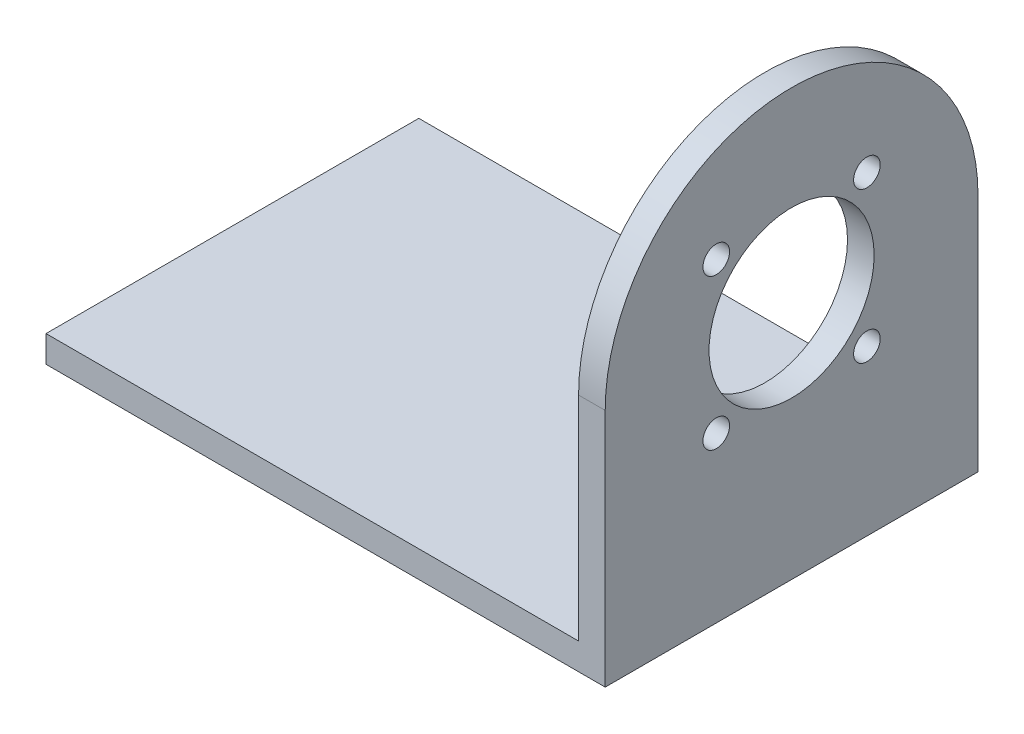
SolidWorks part; units mm, degrees
material "Alloy Steel"
ref_plane "Front Plane" through (0, 0, 0) normal (0, 0, 1) x (1, 0, 0)
ref_plane "Top Plane" through (0, 0, 0) normal (0, 1, 0) x (1, 0, 0)
ref_plane "Right Plane" through (0, 0, 0) normal (1, 0, 0) x (0, 0, -1)
sketch "Sketch1" plane through (0, 0, 0) normal (0, 1, 0) x (1, 0, 0)
  line L1 (-52.5, -35) -> (52.5, -35)
  line L2 (-52.5, -35) -> (-52.5, 35)
  line L3 (-52.5, 35) -> (52.5, 35)
  line L4 (52.5, -35) -> (52.5, 35)
  line L5 (-52.5, -35) -> (52.5, 35) construction
  line L6 (-52.5, 35) -> (52.5, -35) construction
  point P0 (0, 0)
  dimension "D1" = 70
  dimension "D2" = 105
extrude "Boss-Extrude1" add sketch "Sketch1" along normal blind 5
sketch "Sketch2" plane through (0, 5, 0) normal (0, 1, 0) x (1, 0, 0)
  line L0 (-52.5, -35) -> (52.5, -35) construction
  line L1 (52.5, 35) -> (47.5, 35)
  line L2 (52.5, 35) -> (52.5, -35)
  line L3 (52.5, -35) -> (47.5, -35)
  line L4 (47.5, 35) -> (47.5, -35)
  dimension "D1" = 5
extrude "Boss-Extrude2" add sketch "Sketch2" along normal blind 70
sketch "Sketch3" plane through (47.5, 0, 0) normal (-1, 0, 0) x (0, 0, 1)
  line L0 (-35, 75) -> (-35, 5) construction
  line L1 (-35, 75) -> (-35, 45)
  line L2 (35, 75) -> (35, 5) construction
  line L3 (35, 75) -> (35, 45)
  line L4 (0, 29.9331) -> (0, 64.3237) construction
  line L5 (-25.6841, 45) -> (12.1891, 45) construction
  line L6 (-35, 75) -> (35, 75) construction
  line L7 (-35, 75) -> (35, 75)
  arc A0 (35, 45) -> (-35, 45) centre (0, 45) ccw
  line M6 (35, 5) -> (35, 75)
  line M7 (35, 75) -> (-35, 75)
  line M8 (-35, 75) -> (-35, 5)
  dimension "D1" = 70
extrude "Cut-Extrude1" cut sketch "Sketch3" against normal blind 20 contours A0 L7 M8 | A0 M6 M7
sketch "Sketch4" plane through (47.5, 0, 0) normal (-1, 0, 0) x (0, 0, 1)
  circle A0 centre (0, 45) radius 25.5
  dimension "D1" = 51
extrude "Cut-Extrude2" cut sketch "Sketch4" against normal blind 10
sketch "Sketch5" plane through (52.5, 0, 0) normal (1, 0, 0) x (0, 0, -1)
  line L0 (-18.0278, 75) -> (18.0278, 75) construction
  line L1 (-18.0278, 75) -> (18.0278, 75)
  arc A0 (18.0278, 75) -> (-18.0278, 75) centre (0, 45) ccw
extrude "Boss-Extrude3" add sketch "Sketch5" against normal up to surface (5 mm away) up to face at (47.5, 45, 25.5)
sketch "Sketch6" plane through (52.5, 0, 0) normal (1, 0, 0) x (0, 0, -1)
  circle A0 centre (0, 45) radius 15.5
  circle A1 centre (0, 45) radius 25.5 construction
  circle A2 centre (0, 45) radius 25.5
  dimension "D1" = 31
extrude "Boss-Extrude4" add sketch "Sketch6" against normal up to surface (5 mm away) up to face at (47.5, 45, 25.5)
sketch "Sketch7" plane through (52.5, 0, 0) normal (1, 0, 0) x (0, 0, -1)
  line L0 (0, 45) -> (0, 76.2114) construction
  line L1 (0, 45) -> (21.4868, 66.4868) construction
  circle A0 centre (0, 45) radius 20 construction
  circle A1 centre (14.1421, 59.1421) radius 2.5
  circle A2 centre (14.1421, 30.8579) radius 2.5
  circle A3 centre (-14.1421, 30.8579) radius 2.5
  circle A4 centre (-14.1421, 59.1421) radius 2.5
  point P17 (0, 45)
  dimension "D1" = 40
  dimension "D3" = 5
  dimension "D2" = 45
  dimension "D4" = 4
extrude "Cut-Extrude3" cut sketch "Sketch7" against normal up to surface (5 mm away) up to face at (47.5, 33.75, 0)
